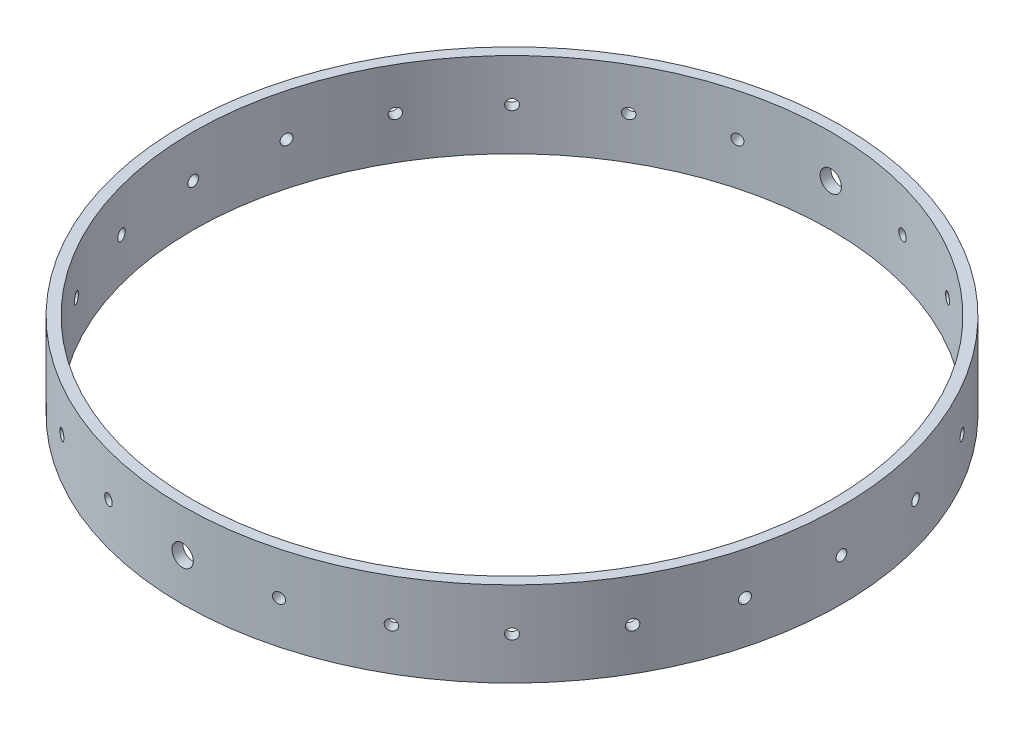
SolidWorks part; units mm, degrees
ref_plane "Front Plane" through (0, 0, 0) normal (0, 0, 1) x (1, 0, 0)
ref_plane "Top Plane" through (0, 0, 0) normal (0, 1, 0) x (1, 0, 0)
ref_plane "Right Plane" through (0, 0, 0) normal (1, 0, 0) x (0, 0, -1)
sketch "Sketch1" plane through (0, 0, 0) normal (0, 1, 0) x (1, 0, 0)
  circle A0 centre (0, 0) radius 98.425
  circle A1 centre (0, 0) radius 95.25
  dimension "D1" = 196.85
  dimension "D2" = 190.5
extrude "Boss-Extrude1" add sketch "Sketch1" along normal blind 25.4
sketch "Sketch2" plane through (0, 0, 0) normal (0, 0, 1) x (1, 0, 0)
  circle A0 centre (0, 12.7) radius 3.175
  dimension "D1" = 6.35
extrude "Cut-Extrude1" cut sketch "Sketch2" against normal through all and the other way through all
sketch "Sketch3" plane through (0, 0, 0) normal (1, 0, 0) x (0, 0, -1)
  circle A0 centre (0, 12.7) radius 1.5875
  dimension "D1" = 3.175
extrude "Cut-Extrude3" cut sketch "Sketch3" against normal through all
sketch "Sketch4" plane through (0, 0, 0) normal (1, 0, 0) x (0, 0, -1)
  line L0 (0, 0) -> (0, 72.5565) construction
pattern_circular "CirPattern1" count 24 over 360 about axis through (0, 0, 0) along (0, 1, 0) of "Cut-Extrude3"
